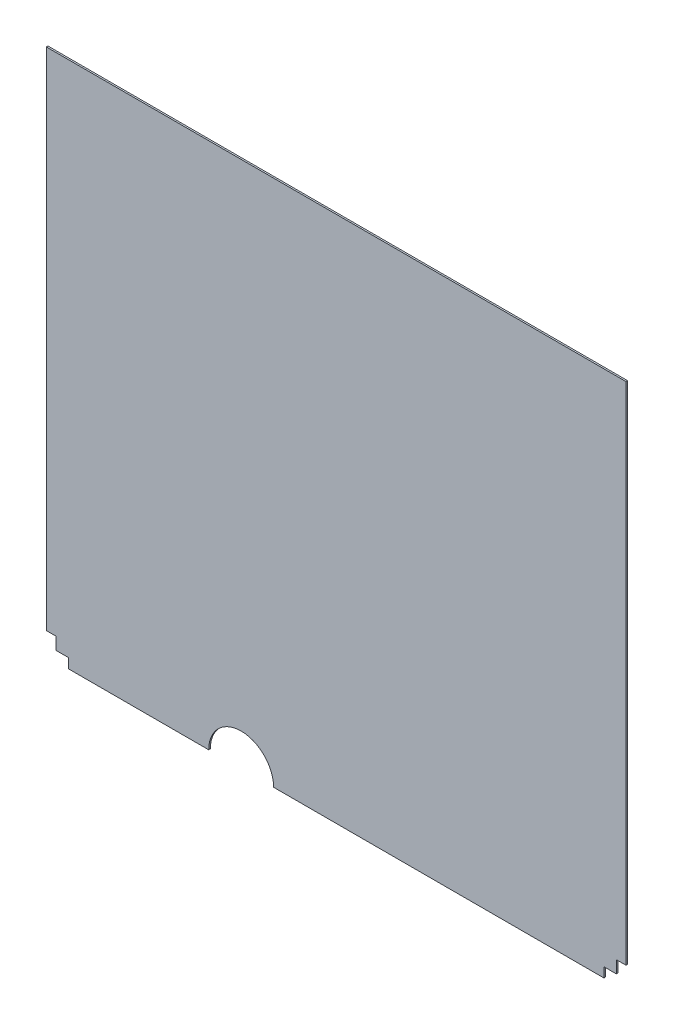
SolidWorks part; units mm, degrees
ref_plane "Front Plane" through (0, 0, 0) normal (0, 0, 1) x (1, 0, 0)
ref_plane "Top Plane" through (0, 0, 0) normal (0, 1, 0) x (1, 0, 0)
ref_plane "Right Plane" through (0, 0, 0) normal (1, 0, 0) x (0, 0, -1)
sketch "Sketch1" plane through (0, 0, 0) normal (0, 0, 1) x (1, 0, 0)
  line L0 (0, 34.544) -> (15.24, 34.544)
  line L1 (0, 0) -> (907.001, 0)
  line L2 (0, 0) -> (0, 825.5)
  line L3 (0, 825.5) -> (907.001, 825.5)
  line L4 (907.001, 0) -> (907.001, 825.5)
  line L5 (0, 0) -> (914.4, 0) construction
  line L6 (0, 0) -> (0, 914.4) construction
  line L7 (0, 914.4) -> (914.4, 914.4) construction
  line L8 (914.4, 0) -> (914.4, 914.4) construction
  line L9 (15.24, 34.544) -> (15.24, 15.24)
  line L10 (15.24, 15.24) -> (34.544, 15.24)
  line L11 (34.544, 15.24) -> (34.544, 0)
  line L12 (907.001, 34.544) -> (891.761, 34.544)
  line L13 (891.761, 34.544) -> (891.761, 15.24)
  line L14 (891.761, 15.24) -> (872.457, 15.24)
  line L15 (872.457, 15.24) -> (872.457, 0)
  arc A0 (355.6, 0) -> (254, 0) centre (304.8, 0) ccw
  dimension "D13" = 50.8
  dimension "D1" = 825.5
  dimension "D2" = 907.001
  dimension "D3" = 914.4
  dimension "D4" = 914.4
  dimension "D5" = 15.24
  dimension "D6" = 15.24
  dimension "D7" = 34.544
  dimension "D8" = 34.544
  dimension "D9" = 15.24
  dimension "D10" = 15.24
  dimension "D11" = 34.544
  dimension "D12" = 34.544
  dimension "D14" = 304.8
extrude "Boss-Extrude1" add sketch "Sketch1" along normal blind 2.54 contours L15 L14 L13 L12 L4 L3 L2 L0 L9 L10 L11 L1
